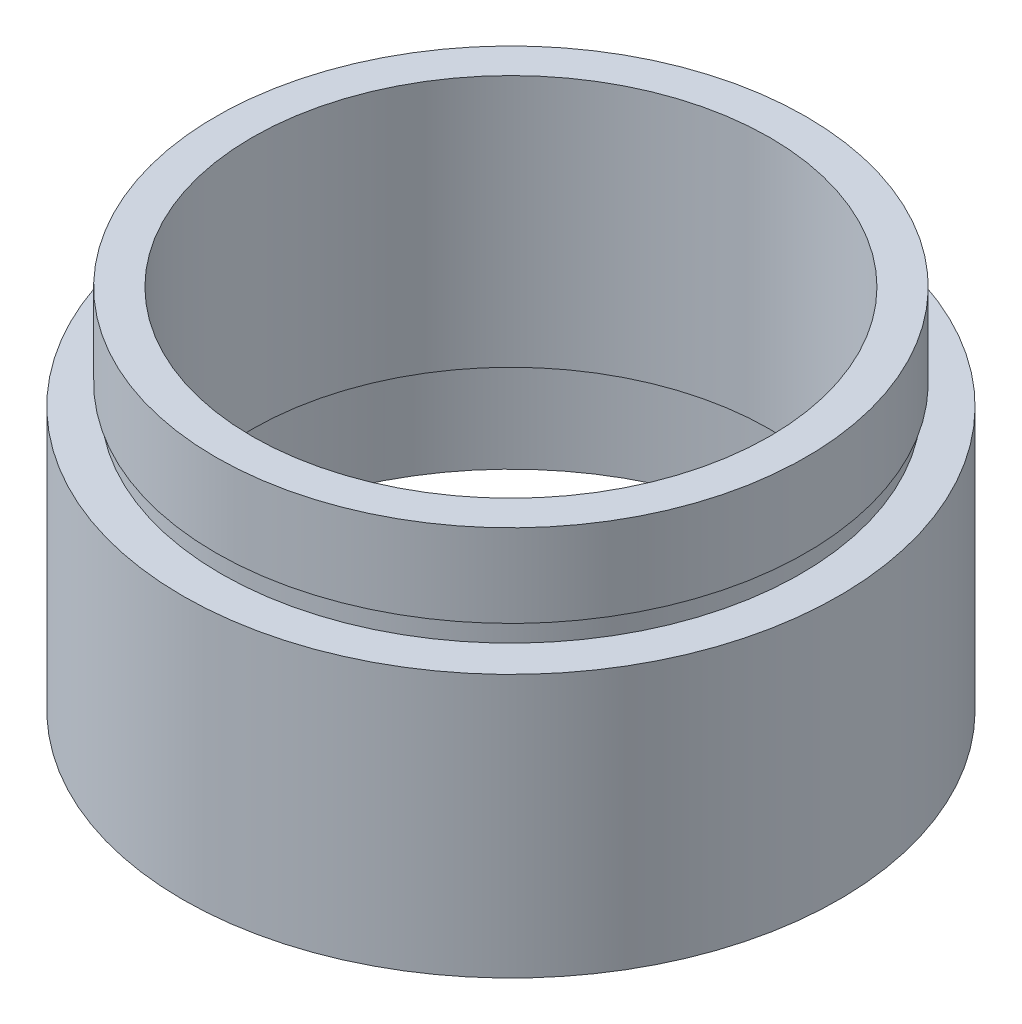
SolidWorks part; units mm, degrees
ref_plane "前视基准面" through (0, 0, 0) normal (0, 0, 1) x (1, 0, 0)
ref_plane "上视基准面" through (0, 0, 0) normal (0, 1, 0) x (1, 0, 0)
ref_plane "右视基准面" through (0, 0, 0) normal (1, 0, 0) x (0, 0, -1)
sketch "草图1" plane through (0, 0, 0) normal (0, 0, 1) x (1, 0, 0)
  line L0 (0, 161.3762) -> (0, 0) construction
  line L1 (141.7365, 0) -> (-131.7984, 0) construction
  line L2 (14.25, 0) -> (14.25, 4.5)
  line L3 (15.85, 0) -> (15.85, 12.7)
  line L4 (14.25, 0) -> (15.85, 0)
  line L5 (14.35, 4.5) -> (14.35, 5.5)
  line L6 (14.25, 4.5) -> (14.35, 4.5)
  line L7 (12.5, 5.5) -> (12.5, 17.7)
  line L8 (12.5, 5.5) -> (14.35, 5.5)
  line L9 (14.25, 17.7) -> (14.25, 13.7)
  line L10 (12.5, 17.7) -> (14.25, 17.7)
  line L11 (14, 13.7) -> (14, 12.7)
  line L12 (14, 13.7) -> (14.25, 13.7)
  line L13 (14, 12.7) -> (15.85, 12.7)
  point P7 (14.25, 2.25)
  dimension "D1" = 14.25
  dimension "D2" = 4.5
  dimension "D3" = 15.85
  dimension "D4" = 14.35
  dimension "D5" = 12.5
  dimension "D6" = 1
  dimension "D7" = 12.7
  dimension "D8" = 14.25
  dimension "D9" = 14
  dimension "D10" = 5
  dimension "D11" = 1
revolve "旋转1" add sketch "草图1" angle 360 about L0
cosmetic thread "装饰螺纹线1" parameters "D2"=28.51
cosmetic thread "装饰螺纹线2" parameters "D2"=26
cosmetic thread "装饰螺纹线3" parameters "D2"=28.49
